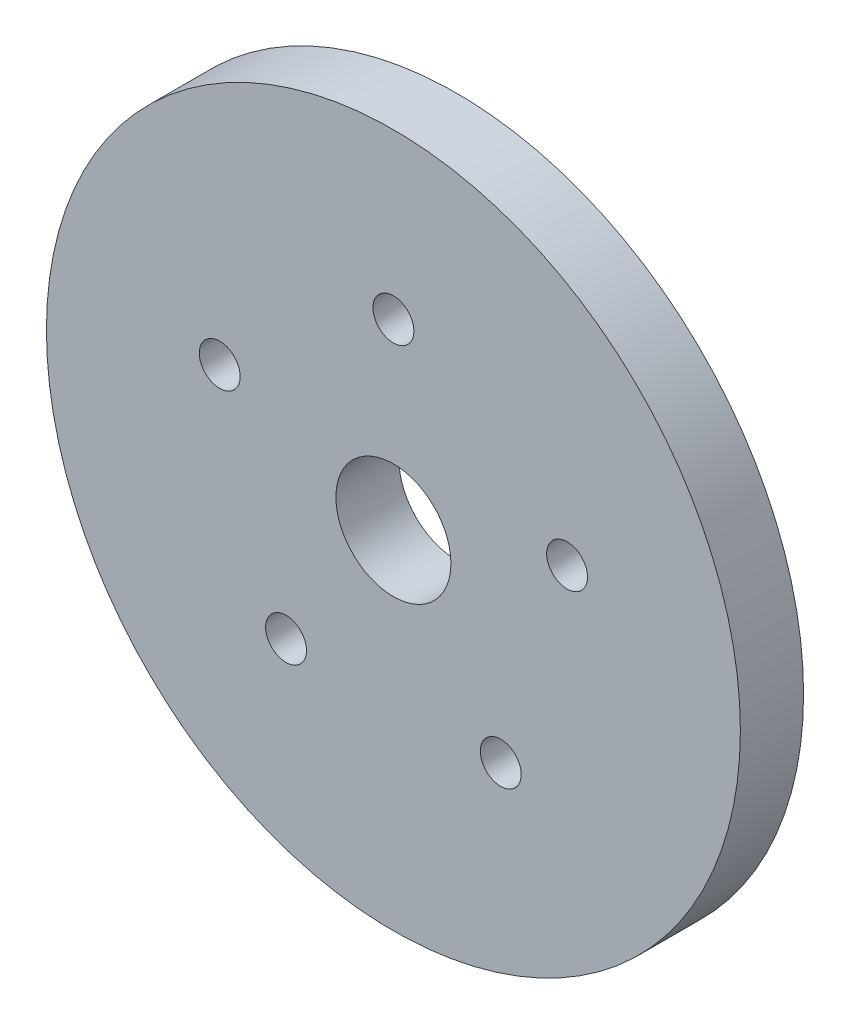
SolidWorks part; units mm, degrees
ref_plane "Front Plane" through (0, 0, 0) normal (0, 0, 1) x (1, 0, 0)
ref_plane "Top Plane" through (0, 0, 0) normal (0, 1, 0) x (1, 0, 0)
ref_plane "Right Plane" through (0, 0, 0) normal (1, 0, 0) x (0, 0, -1)
sketch "Sketch1" plane through (0, 0, 0) normal (0, 0, 1) x (1, 0, 0)
  line L0 (0, 0) -> (0, 24.13) construction
  circle A0 centre (0, 0) radius 24.13
  circle A1 centre (0, 12.7) radius 1.4224
  circle A2 centre (12.0784, 3.9245) radius 1.4224
  circle A3 centre (7.4649, -10.2745) radius 1.4224
  circle A4 centre (-7.4649, -10.2745) radius 1.4224
  circle A5 centre (-12.0784, 3.9245) radius 1.4224
  circle A6 centre (0, 0) radius 4
  point P17 (0, 0)
  dimension "D1" = 48.26
  dimension "D2" = 2.8448
  dimension "D5" = 8
  dimension "D3" = 12.7
  dimension "D4" = 5
extrude "Boss-Extrude1" add sketch "Sketch1" along normal blind 4.3942
